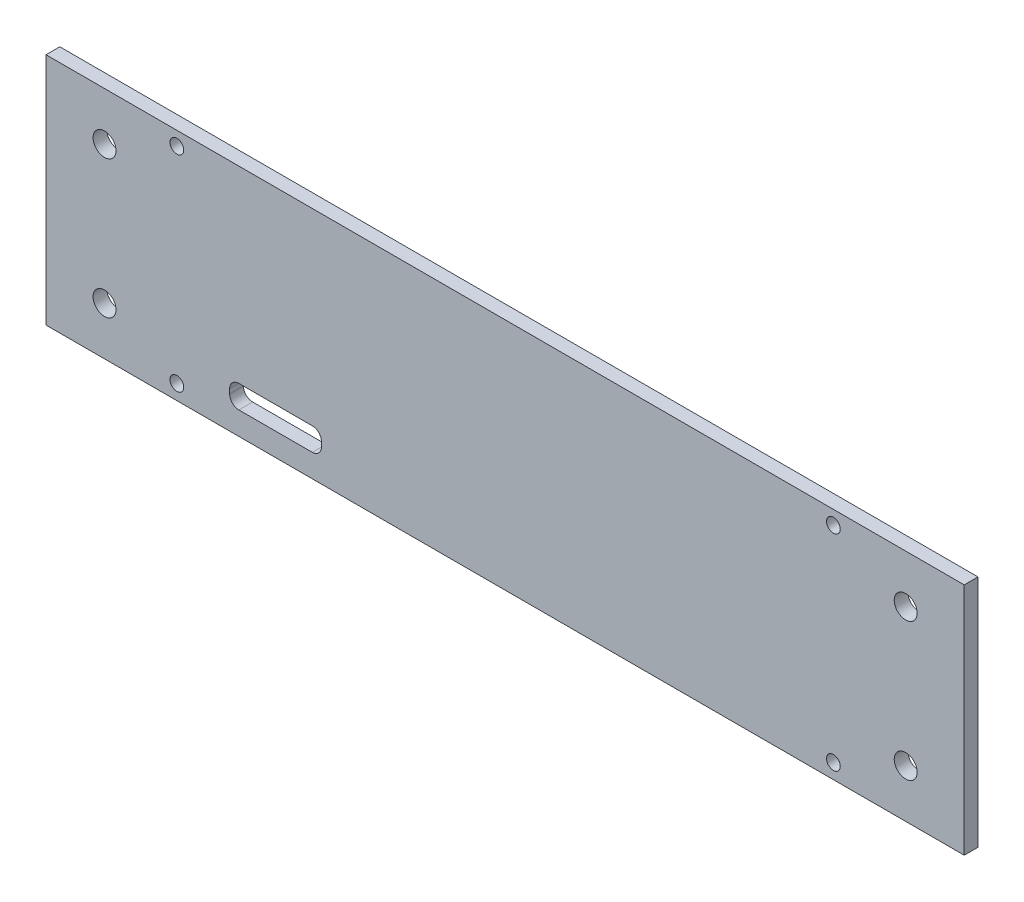
SolidWorks part; units mm, degrees
material "PET"
ref_plane "Front Plane" through (0, 0, 0) normal (0, 0, 1) x (1, 0, 0)
ref_plane "Top Plane" through (0, 0, 0) normal (0, 1, 0) x (1, 0, 0)
ref_plane "Right Plane" through (0, 0, 0) normal (1, 0, 0) x (0, 0, -1)
sketch "Sketch1" plane through (0, 0, 0) normal (0, 0, 1) x (1, 0, 0)
  line L1 (0, 0) -> (200, 0)
  line L2 (0, 0) -> (0, 51)
  line L3 (0, 51) -> (200, 51)
  line L4 (200, 0) -> (200, 51)
  dimension "D1" = 200
  dimension "D2" = 51
extrude "Boss-Extrude1" add sketch "Sketch1" along normal blind 3 contours L2 L1 L4 L3
sketch "Sketch2" plane through (0, 0, 3) normal (0, 0, 1) x (1, 0, 0)
  line L0 (100, 51) -> (100, 0) construction
  line L1 (0, 51) -> (200, 51) construction
  line L2 (0, 0) -> (200, 0) construction
  line L3 (28.5, 51) -> (28.5, 0) construction
  line L4 (12.75, 51) -> (12.75, 0) construction
  line L5 (0, 0) -> (0, 51) construction
  line L6 (187.25, 51) -> (187.25, 0) construction
  line L7 (171.5, 51) -> (171.5, 0) construction
  circle A0 centre (28.5, 48) radius 1.5
  circle A1 centre (28.5, 3.25) radius 1.5
  circle A2 centre (12.75, 40.5) radius 2.5
  circle A3 centre (12.75, 10.5) radius 2.5
  circle A4 centre (187.25, 40.5) radius 2.5
  circle A5 centre (187.25, 10.5) radius 2.5
  circle A6 centre (171.5, 3.25) radius 1.5
  circle A7 centre (171.5, 48) radius 1.5
  dimension "D2" = 44.75
  dimension "D3" = 3
  dimension "D5" = 30
  dimension "D6" = 5
  dimension "D7" = 10.5
  dimension "D8" = 3
  dimension "D1" = 71.5
  dimension "D4" = 12.75
extrude "Cut-Extrude1" cut sketch "Sketch2" against normal up to surface (3 mm away) up to face at (100, 25.5, 0)
sketch "Sketch3" plane through (0, 0, 3) normal (0, 0, 1) x (1, 0, 0)
  line L0 (100, 51) -> (100, 0) construction
  line L1 (0, 51) -> (200, 51) construction
  line L2 (0, 0) -> (200, 0) construction
  line L4 (40, 10) -> (60, 10)
  line L5 (40, 10) -> (40, 5)
  line L6 (40, 5) -> (60, 5)
  line L7 (60, 10) -> (60, 5)
  dimension "D1" = 20
  dimension "D2" = 5
  dimension "D3" = 40
  dimension "D4" = 5
extrude "Cut-Extrude2" cut sketch "Sketch3" against normal up to surface (3 mm away) up to face at (189.75, 40.5, 0)
fillet "Fillet1" radius 2 4 edges at (60, 10, 1.5) (60, 5, 1.5) (40, 5, 1.5) (40, 10, 1.5)
